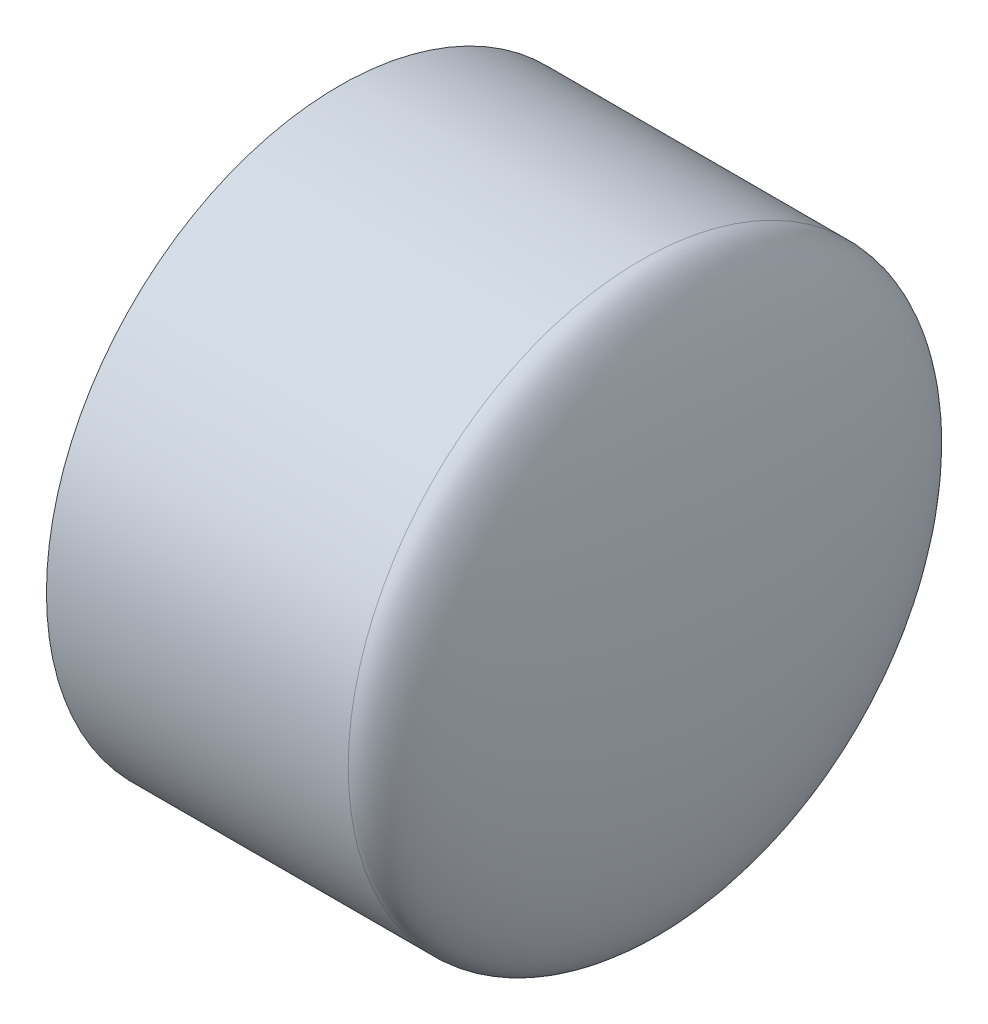
SolidWorks part; units mm, degrees
ref_plane "Front Plane" through (0, 0, 0) normal (0, 0, 1) x (1, 0, 0)
ref_plane "Top Plane" through (0, 0, 0) normal (0, 1, 0) x (1, 0, 0)
ref_plane "Right Plane" through (0, 0, 0) normal (1, 0, 0) x (0, 0, -1)
sketch "Sketch0" plane through (0, 0, 0) normal (0, 0, 1) x (1, 0, 0)
  line L0 (-80.9625, 0) -> (0, 0) construction
  line L2 (-30.1625, 0) -> (0, 0) construction
  line L4 (-80.9625, 63.8969) -> (-80.9625, -63.8969) construction
  line L5 (-30.1625, 57.0357) -> (-80.9625, 57.3786) construction
  line L6 (-30.1625, 57.0357) -> (-30.1625, -57.0357) construction
  line L7 (-30.1625, -57.0357) -> (-80.9625, -57.3786) construction
  line L8 (-80.9625, 57.3786) -> (-80.9625, -57.3786) construction
  line L14 (-30.1625, 51.1302) -> (-30.1625, -51.1302) construction
  dimension "M" = 127.7937
  dimension "OD A" = 114.7572
  dimension "OD B" = 114.0714
  dimension "ID" = 102.2604
  dimension "L" = 80.9625
  dimension "C" = 50.8
sketch "Sketch1" plane through (0, 0, 0) normal (0, 0, 1) x (1, 0, 0)
  line L0 (-80.9625, 0) -> (0, 0) construction
  line L1 (-80.9625, 0) -> (0, 0) construction
  line L2 (-15.0812, 0) -> (0, 0)
  line L3 (-80.9625, -63.8969) -> (-15.0812, -63.8969)
  line L4 (-80.9625, -63.8969) -> (-80.9625, -57.3786)
  line L5 (-80.9625, -57.3786) -> (-30.1625, -57.0357)
  line L7 (-15.0812, 0) -> (-15.0812, -63.8969) construction
  ellipse E0 centre (-15.0812, 0) end of major axis (-15.0812, -63.8969) minor radius 15.0812 (-15.0812, -63.8969) -> (0, 0) ccw
  ellipse E1 centre (-30.1625, 0) end of major axis (-30.1625, -57.0357) minor radius 15.0812 (-30.1625, -57.0357) -> (-15.0812, 0) ccw
revolve "Revolve1" add sketch "Sketch1" angle 360 about L1
